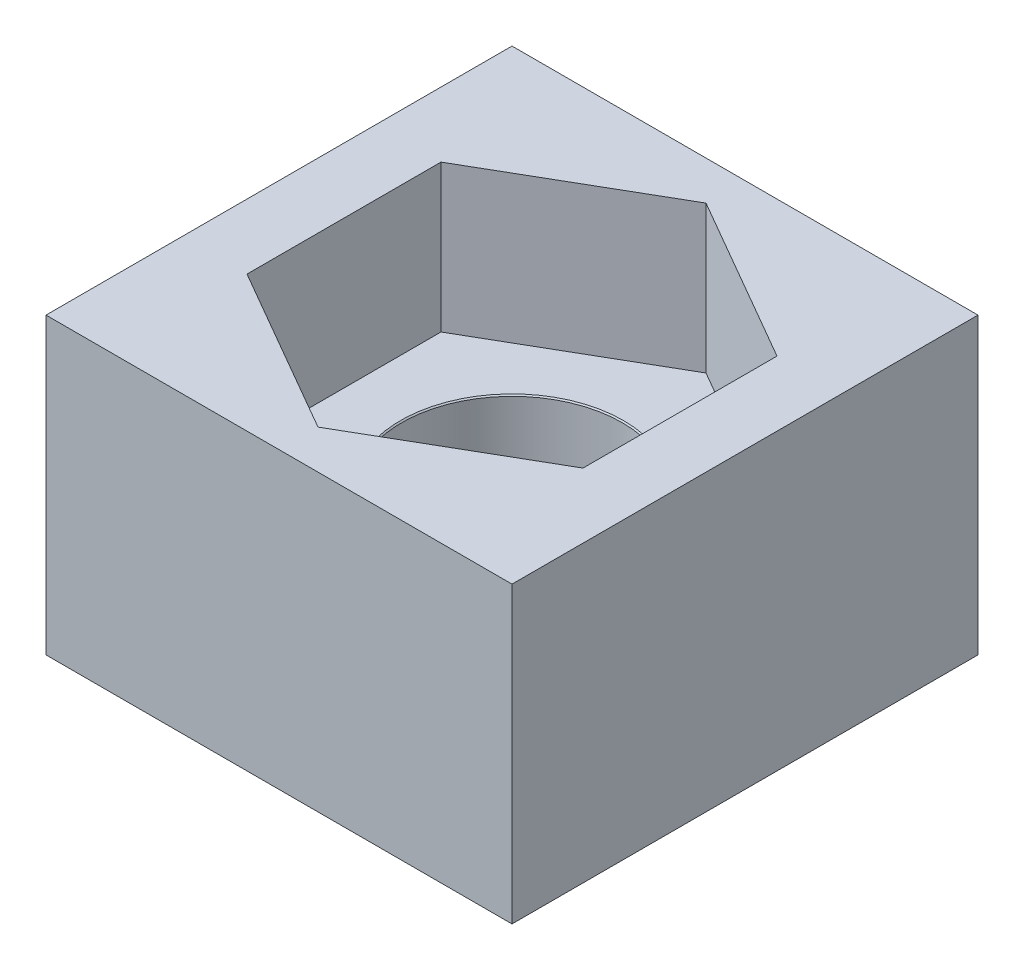
SolidWorks part; units mm, degrees
ref_plane "Front Plane" through (0, 0, 0) normal (0, 0, 1) x (1, 0, 0)
ref_plane "Top Plane" through (0, 0, 0) normal (0, 1, 0) x (1, 0, 0)
ref_plane "Right Plane" through (0, 0, 0) normal (1, 0, 0) x (0, 0, -1)
sketch "Sketch1" plane through (0, 0, 0) normal (0, 1, 0) x (1, 0, 0)
  line L1 (4.75, 4.75) -> (-4.75, 4.75)
  line L2 (4.75, 4.75) -> (4.75, -4.75)
  line L3 (4.75, -4.75) -> (-4.75, -4.75)
  line L4 (-4.75, 4.75) -> (-4.75, -4.75)
  line L5 (4.75, 4.75) -> (-4.75, -4.75) construction
  line L6 (4.75, -4.75) -> (-4.75, 4.75) construction
  point P0 (0, 0)
  dimension "D1" = 9.5
extrude "Boss-Extrude1" add sketch "Sketch1" along normal blind 6 contours L4 L3 L2 L1
sketch "Sketch2" plane through (0, 6, 0) normal (0, 1, 0) x (1, 0, 0)
  line L1 (0, -3.9548) -> (3.425, -1.9774)
  line L2 (3.425, -1.9774) -> (3.425, 1.9774)
  line L3 (3.425, 1.9774) -> (0, 3.9548)
  line L4 (0, 3.9548) -> (-3.425, 1.9774)
  line L5 (-3.425, 1.9774) -> (-3.425, -1.9774)
  line L6 (-3.425, -1.9774) -> (0, -3.9548)
  circle A0 centre (0, 0) radius 3.425 construction
  dimension "D1" = 6.85
extrude "Cut-Extrude1" cut sketch "Sketch2" against normal blind 3
hole_wizard "M4 Clearance Hole1" positions "Sketch4" profile "Sketch5" hole size "M4" standard "ANSI Metric" end condition through all
sketch "Sketch4" plane through (0, 3, 0) normal (0, 1, 0) x (1, 0, 0)
  point P0 (0, 0)
sketch "Sketch5" plane through (0, 3, 0) normal (1, 0, 0) x (0, 0, 1)
  line L0 (0, 0) -> (0, 3)
  line L1 (0, 3) -> (2.25, 3)
  line L2 (2.25, 3) -> (2.25, 0.025)
  line L3 (2.25, 0.025) -> (2.275, 0)
  line L5 (2.275, 0) -> (0, 0)
  line L6 (-2.25, 0.025) -> (-2.275, 0) construction
  line L11 (0, -6.35) -> (0, 107.95) construction
  dimension "Thru Hole Dia." = 4.5
  dimension "Thru Hole Depth" = 3
  dimension "Near C'Sink Dia." = 4.55
  dimension "Near C'Sink Angle" = 90
